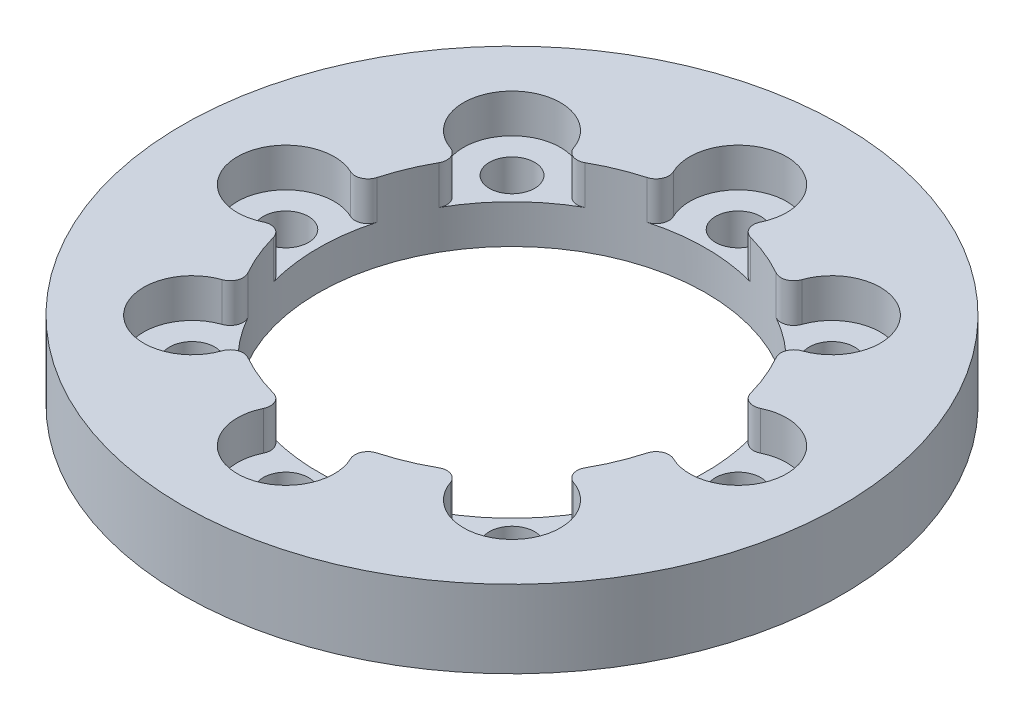
SolidWorks part; units mm, degrees
ref_plane "Front Plane" through (0, 0, 0) normal (0, 0, 1) x (1, 0, 0)
ref_plane "Top Plane" through (0, 0, 0) normal (0, 1, 0) x (1, 0, 0)
ref_plane "Right Plane" through (0, 0, 0) normal (1, 0, 0) x (0, 0, -1)
sketch "Sketch1" plane through (0, 0, 0) normal (0, 1, 0) x (1, 0, 0)
  circle A0 centre (0, 0) radius 25.5
  circle A1 centre (0, 0) radius 15
  circle A2 centre (0, 17.5) radius 1.75
  circle A3 centre (12.3744, 12.3744) radius 1.75
  circle A4 centre (17.5, 0) radius 1.75
  circle A5 centre (12.3744, -12.3744) radius 1.75
  circle A6 centre (0, -17.5) radius 1.75
  circle A7 centre (-12.3744, -12.3744) radius 1.75
  circle A8 centre (-17.5, 0) radius 1.75
  circle A9 centre (-12.3744, 12.3744) radius 1.75
  point P22 (0, 0)
  dimension "D1" = 30
  dimension "D2" = 51
  dimension "D4" = 3.5
  dimension "D3" = 17.5
  dimension "D5" = 8
extrude "Boss-Extrude1" add sketch "Sketch1" along normal blind 6
sketch "Sketch2" plane through (0, 6, 0) normal (0, 1, 0) x (1, 0, 0)
  circle A0 centre (-12.3744, 12.3744) radius 3.75
  circle A1 centre (-12.3744, 12.3744) radius 1.75
  circle A2 centre (-12.3744, 12.3744) radius 1.75
  circle A3 centre (-12.3744, -12.3744) radius 1.75
  circle A4 centre (-12.3744, -12.3744) radius 1.75
  circle A5 centre (12.3744, -12.3744) radius 1.75
  circle A6 centre (12.3744, -12.3744) radius 1.75
  circle A7 centre (12.3744, 12.3744) radius 1.75
  circle A8 centre (12.3744, 12.3744) radius 1.75
  circle A9 centre (0, 17.5) radius 1.75
  circle A10 centre (0, 17.5) radius 1.75
  circle A11 centre (17.5, 0) radius 1.75
  circle A12 centre (17.5, 0) radius 1.75
  circle A13 centre (0, -17.5) radius 1.75
  circle A14 centre (0, -17.5) radius 1.75
  circle A15 centre (-17.5, 0) radius 1.75
  circle A16 centre (-17.5, 0) radius 1.75
  circle A17 centre (-12.3744, -12.3744) radius 3.75
  circle A18 centre (12.3744, -12.3744) radius 3.75
  circle A19 centre (12.3744, 12.3744) radius 3.75
  circle A20 centre (0, 17.5) radius 3.75
  circle A21 centre (17.5, 0) radius 3.75
  circle A22 centre (0, -17.5) radius 3.75
  circle A23 centre (-17.5, 0) radius 3.75
  dimension "D1" = 0
  dimension "D2" = 0
  dimension "D3" = 0
  dimension "D4" = 0
  dimension "D5" = 0
  dimension "D6" = 0
  dimension "D7" = 0
  dimension "D8" = 0
  dimension "D9" = 2
extrude "Cut-Extrude1" cut sketch "Sketch2" against normal blind 3
fillet "Fillet1" radius 1 16 edges at (12.2718, 4.5, -8.6258) (8.6258, 4.5, -12.2718) (-14.7768, 4.5, -2.5781) (-14.7768, 4.5, 2.5781) (2.5781, 4.5, -14.7768) (-2.5781, 4.5, -14.7768) (14.7768, 4.5, 2.5781) (14.7768, 4.5, -2.5781) (8.6258, 4.5, 12.2718) (12.2718, 4.5, 8.6258) (-8.6258, 4.5, -12.2718) (-12.2718, 4.5, -8.6258) (-2.5781, 4.5, 14.7768) (2.5781, 4.5, 14.7768) (-12.2718, 4.5, 8.6258) (-8.6258, 4.5, 12.2718)
